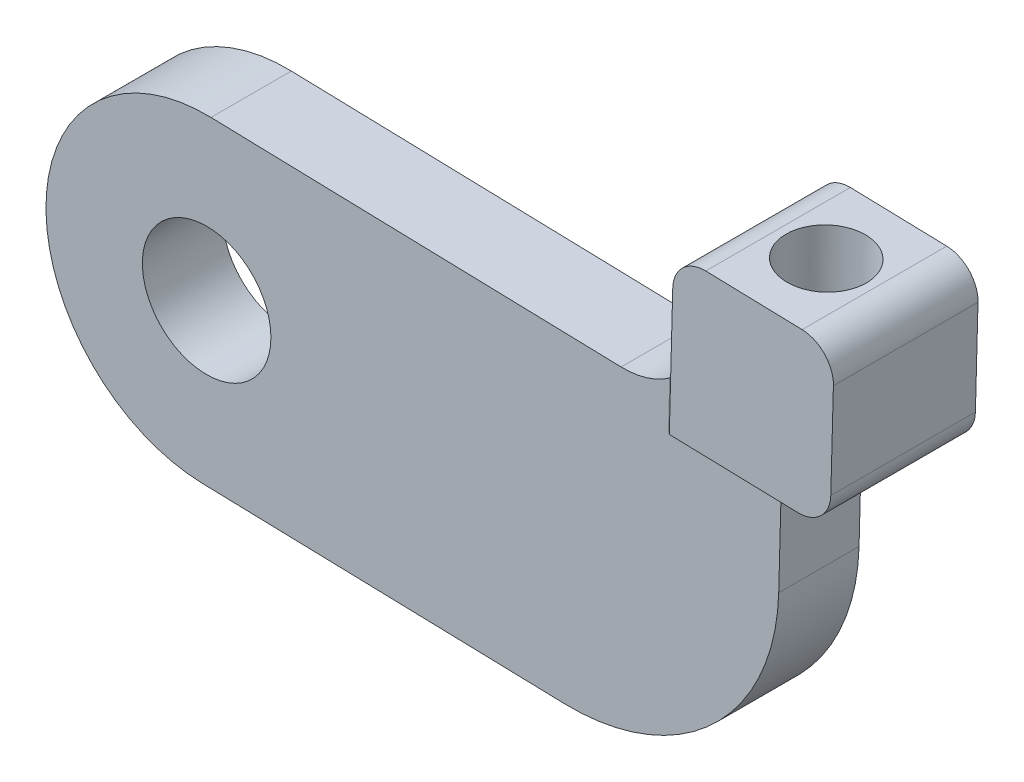
SolidWorks part; units mm, degrees
ref_plane "Front Plane" through (0, 0, 0) normal (0, 0, 1) x (1, 0, 0)
ref_plane "Top Plane" through (0, 0, 0) normal (0, 1, 0) x (1, 0, 0)
ref_plane "Right Plane" through (0, 0, 0) normal (1, 0, 0) x (0, 0, -1)
sketch "Sketch1" plane through (0, 0, 0) normal (0, 0, 1) x (1, 0, 0)
  line L0 (-22.5, 0.6061) -> (22.5, -0.6061) construction
  line L1 (-22.2307, 10.6025) -> (22.7693, 9.3903)
  line L2 (-22.7693, -9.3903) -> (22.2307, -10.6025)
  arc A0 (-22.2307, 10.6025) -> (-22.7693, -9.3903) centre (-22.5, 0.6061) ccw
  arc A1 (22.2307, -10.6025) -> (22.7693, 9.3903) centre (22.5, -0.6061) ccw
  circle A2 centre (22.5, -0.6061) radius 4
  circle A3 centre (-22.5, 0.6061) radius 4
  point P2 (0, 0)
  dimension "D3" = 8
  dimension "D4" = 8
  dimension "D1" = 45
  dimension "D2" = 20
extrude "Boss-Extrude1" add sketch "Sketch1" along normal blind 5
sketch "Sketch2" plane through (0.2693, 9.9964, 0) normal (0.0269, 0.9996, 0) x (0.9996, -0.0269, 0)
  line L1 (13.0263, -14.9724) -> (42.7721, -14.9724)
  line L2 (13.0263, -14.9724) -> (13.0263, 16.0967)
  line L3 (13.0263, 16.0967) -> (42.7721, 16.0967)
  line L4 (42.7721, -14.9724) -> (42.7721, 16.0967)
  line L5 (13.0263, -14.9724) -> (42.7721, 16.0967) construction
  line L6 (13.0263, 16.0967) -> (42.7721, -14.9724) construction
  point P0 (13.0263, -14.9724)
extrude "Cut-Extrude1" cut sketch "Sketch2" against normal through all
sketch "Sketch3" plane through (0.2693, 9.9964, 0) normal (0.0269, 0.9996, 0) x (0.9996, -0.0269, 0)
  line L0 (13.0263, -5) -> (13.0263, 0) construction
  line L1 (8.0263, -10) -> (18.0263, -10)
  line L2 (8.0263, -10) -> (8.0263, 5)
  line L3 (8.0263, 5) -> (18.0263, 5)
  line L4 (18.0263, -10) -> (18.0263, 5)
  line L5 (13.0263, 0) -> (-22.5082, 0) construction
  line L6 (13.0263, -5) -> (-22.5082, -5) construction
  point P4 (5.5414, -7.7361)
  dimension "D1" = 5
  dimension "D2" = 10
  dimension "D3" = 5
  dimension "D4" = 5
extrude "Boss-Extrude2" add sketch "Sketch3" along normal blind 10
fillet "Fillet1" radius 13 1 edges at (12.7523, -10.3471, 2.5)
fillet "Fillet2" radius 5 1 edges at (8.2927, 9.7802, 2.5)
fillet "Fillet3" radius 2 5 edges at (8.36, 12.2793, 5) (10.7917, 9.7129, 5) (13.2908, 9.6456, 2.5) (8.36, 12.2793, 0) (10.7917, 9.7129, 0)
fillet "Fillet4" radius 2 9 edges at (8.4273, 14.7784, 10) (13.5601, 19.642, 10) (18.289, 9.511, 2.5) (18.4237, 14.5091, 10) (8.4273, 14.7784, -5) (13.5601, 19.642, -5) (18.4237, 14.5091, -5) (18.5583, 19.5073, 2.5) (8.5619, 19.7766, 2.5)
sketch "Sketch4" plane through (0.5386, 19.9927, 0) normal (0.0269, 0.9996, 0) x (0.9996, -0.0269, 0)
  line L0 (16.0263, -8) -> (16.0263, 3) construction
  line L1 (16.0263, 3) -> (10.0263, 3) construction
  circle A0 centre (13.0263, -2.5) radius 2.5
  point P4 (16.0263, -2.5)
  point P7 (13.0263, 3)
  dimension "D1" = 5
extrude "Cut-Extrude2" cut sketch "Sketch4" against normal blind 7
sketch "Sketch6" plane through (18.0197, -0.4854, 0) normal (0.9996, -0.0269, 0) x (0, 0, -1)
  line L0 (3, 12) -> (3, 18) construction
  line L1 (2, 6.3314) -> (7.48, 6.3314)
  line L2 (2, 6.3314) -> (2, 22.7531)
  line L3 (2, 22.7531) -> (7.48, 22.7531)
  line L4 (7.48, 6.3314) -> (7.48, 22.7531)
  line L5 (-2.5, 18) -> (-2.5, 11.4338) construction
  line L6 (3, 18) -> (-8, 18) construction
  line L7 (-12.48, 6.3314) -> (-12.48, 22.7531)
  line L8 (-7, 22.7531) -> (-12.48, 22.7531)
  line L9 (-7, 6.3314) -> (-7, 22.7531)
  line L10 (-7, 6.3314) -> (-12.48, 6.3314)
  dimension "D1" = 1
extrude "Cut-Extrude3" cut sketch "Sketch6" against normal through all
